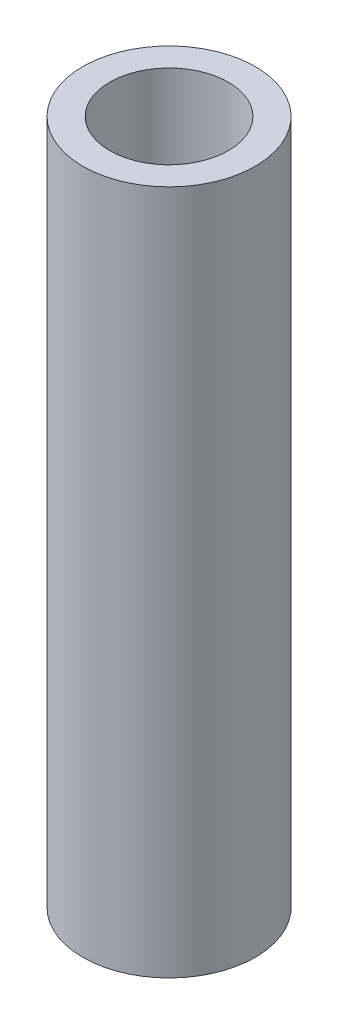
SolidWorks part; units mm, degrees
ref_plane "Front Plane" through (0, 0, 0) normal (0, 0, 1) x (1, 0, 0)
ref_plane "Top Plane" through (0, 0, 0) normal (0, 1, 0) x (1, 0, 0)
ref_plane "Right Plane" through (0, 0, 0) normal (1, 0, 0) x (0, 0, -1)
sketch "Sketch1" plane through (0, 0, 0) normal (0, 1, 0) x (1, 0, 0)
  circle A0 centre (0, 0) radius 3.2
  circle A1 centre (0, 0) radius 2.2
  dimension "D1" = 6.4
  dimension "D2" = 4.4
extrude "Boss-Extrude1" add sketch "Sketch1" along normal blind 25.4
